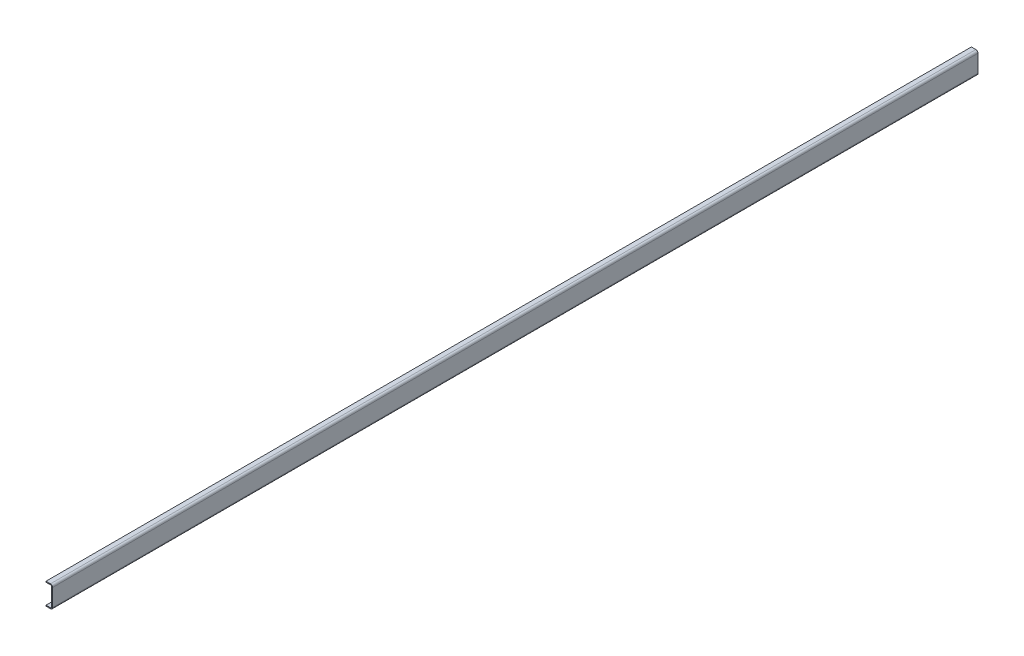
SolidWorks part; units mm, degrees
material "ASTM A572, GR50"
ref_plane "Edge of Rail 1" through (0, 0, 0) normal (0, 0, 1) x (1, 0, 0)
ref_plane "Bottom Flange" through (0, 0, 0) normal (0, 1, 0) x (1, 0, 0)
ref_plane "Outside Web" through (0, 0, 0) normal (1, 0, 0) x (0, 0, -1)
ref_plane "Top Flange" through (0, 228.6, 0) normal (0, 1, 0) x (-1, 0, 0)
ref_plane "Edge of Rail 2" through (0, 0, -9779) normal (0, 0, 1) x (1, 0, 0)
ref_plane "Inside Flange Edge" through (-69.85, 0, 0) normal (1, 0, 0) x (0, 0, -1)
sketch "Sketch1" plane through (0, 0, 0) normal (0, 0, 1) x (1, 0, 0)
  line L0 (50, 228.6) -> (-50, 228.6) construction
  line L1 (-69.85, 0) -> (0, 0)
  line L2 (-69.85, -50) -> (-69.85, 50) construction
  line L3 (-69.85, 228.6) -> (0, 228.6)
  line L4 (0, 0) -> (0, 228.6)
extrude "Base-Extrude-Thin" add sketch "Sketch1" against normal up to surface (9779 mm away) thin up to plane "Edge of Rail 2" thin type one direction wall 9.525
fillet "Inside Bend Radius" radius 12.7 2 edges at (-9.525, 219.075, -4889.5) (-9.525, 9.525, -4889.5)
fillet "Outside Bend Radius" radius 22.225 2 edges at (0, 0, -4889.5) (0, 228.6, -4889.5)
equation "\"OUTSIDE_RADIUS@Outside Bend Radius\" = \"INSIDE_RADIUS@Inside Bend Radius\"+\"THICKNESS@Base-Extrude-Thin\""
